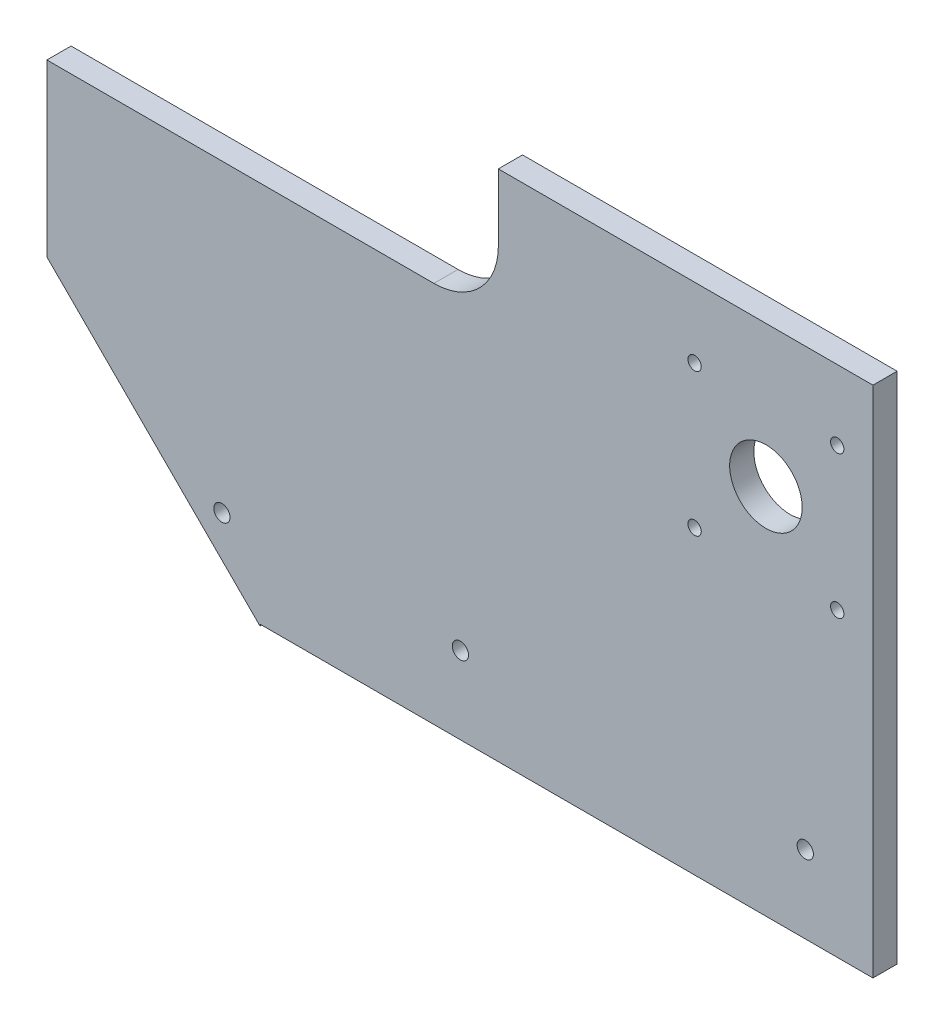
SolidWorks part; units mm, degrees
ref_plane "Front Plane" through (0, 0, 0) normal (0, 0, 1) x (1, 0, 0)
ref_plane "Top Plane" through (0, 0, 0) normal (0, 1, 0) x (1, 0, 0)
ref_plane "Right Plane" through (0, 0, 0) normal (1, 0, 0) x (0, 0, -1)
sketch "Sketch1" plane through (0, 0, 0) normal (0, 0, 1) x (1, 0, 0)
  line L0 (-138.2594, 48.9915) -> (32.2106, -121.4785)
  line L1 (32.2106, -121.4785) -> (222.7106, -121.4785)
  line L2 (-138.2594, 149.5088) -> (-138.2594, 48.9915)
  line L3 (-138.2594, 149.5088) -> (222.7106, 149.5088)
  line L4 (222.7106, -121.4785) -> (222.7106, 149.5088)
  circle A0 centre (180.538, 76.832) radius 14.2875
  circle A2 centre (180.538, 76.832) radius 69.85 construction
  circle A3 centre (180.538, 76.832) radius 318.7974 construction
  point P0 (0, 0)
  point P2 (180.538, 76.832)
  dimension "D4" = 198.3105
  dimension "D1" = 45
  dimension "D2" = 270.9874
  dimension "D5" = 245.11
extrude "Boss-Extrude1" add sketch "Sketch1" along normal blind 9.525
sketch "Sketch2" plane through (0, 0, 9.525) normal (0, 0, 1) x (1, 0, 0)
  line L0 (32.2106, -121.4785) -> (222.7106, -121.4785) construction
  line L1 (241.7606, -121.4785) -> (-18.8123, -121.4785)
  line L2 (241.7606, -121.4785) -> (241.7606, -69.7895)
  line L3 (241.7606, -69.7895) -> (-18.8123, -69.7895)
  line L4 (-18.8123, -121.4785) -> (-18.8123, -69.7895)
extrude "Cut-Extrude1" cut sketch "Sketch2" against normal through all contours L3 L4 L1 L2
sketch "Sketch4" plane through (0, 0, 9.525) normal (0, 0, 1) x (1, 0, 0)
  line L1 (-138.2594, 149.5088) -> (-138.2594, 48.9915) construction
  line L3 (-138.2594, 149.5088) -> (75.1006, 149.5088)
  line L4 (-138.2594, 149.5088) -> (-138.2594, 80.7415)
  line L5 (-138.2594, 80.7415) -> (75.1006, 80.7415)
  line L6 (75.1006, 149.5088) -> (75.1006, 80.7415)
extrude "Cut-Extrude2" cut sketch "Sketch4" against normal through all contours L5 L6 L3 L4
fillet "Fillet2" radius 25.4 2 edges at (-138.2594, 80.7415, 4.7625) (75.1006, 80.7415, 4.7625)
sketch "Sketch16" plane through (222.7106, 0, 0) normal (1, 0, 0) x (0, 0, -1)
  line L0 (0, -69.7895) -> (0, 149.5088) construction
  line L1 (-9.525, 149.5088) -> (0, 149.5088)
  line L2 (-9.525, 149.5088) -> (-9.525, 145.2215)
  line L3 (-9.525, 145.2215) -> (0, 145.2215)
  line L4 (0, 149.5088) -> (0, 145.2215)
extrude "Cut-Extrude3" cut sketch "Sketch16" against normal through all
sketch "Sketch17" plane through (0, 0, 0) normal (0, 0, -1) x (-1, 0, 0)
  line L0 (-222.7106, -69.7895) -> (-222.7106, 145.2215) construction
  line L1 (-75.1006, 145.2215) -> (-222.7106, 145.2215)
  line L2 (-75.1006, 145.2215) -> (-75.1006, 132.5215)
  line L3 (-75.1006, 132.5215) -> (-222.7106, 132.5215)
  line L4 (-222.7106, 145.2215) -> (-222.7106, 132.5215)
  dimension "D1" = 12.7
extrude "Cut-Extrude4" cut sketch "Sketch17" against normal through all
hole_wizard "Tap Drill for M6x0.75 Tap1" positions "Sketch19" profile "Sketch18" hole size "M6x0.75" standard "Lanco STD" end condition through all
sketch "Sketch19" plane through (0, 0, 9.525) normal (0, 0, 1) x (1, 0, 0)
  point P0 (208.638, 104.932)
  point P3 (152.438, 104.932)
  point P6 (152.438, 48.732)
  point P9 (208.638, 48.732)
sketch "Sketch18" plane through (208.638, 104.932, 9.525) normal (1, 0, 0) x (0, -1, 0)
  line L0 (0, 0) -> (0, 9.525)
  line L1 (0, 9.525) -> (2.625, 9.525)
  line L2 (2.625, 9.525) -> (2.625, 0)
  line L5 (2.625, 0) -> (0, 0)
  line L11 (0, -6.35) -> (0, 107.95) construction
  dimension "Thru Hole Dia." = 5.25
  dimension "Thru Hole Depth" = 9.525
hole_wizard "Ø6.4 (6.4) Diameter Hole1" positions "Sketch21" profile "Sketch20" hole size "Ø6.4" standard "ANSI Metric" end condition through all
sketch "Sketch21" plane through (0, 0, 9.525) normal (0, 0, 1) x (1, 0, 0)
  point P0 (196.0406, -39.3145)
  point P2 (60.1506, -39.3145)
  point P4 (-33.8294, -39.3145)
sketch "Sketch20" plane through (196.0406, -39.3145, 9.525) normal (1, 0, 0) x (0, -1, 0)
  line L0 (0, 0) -> (0, 9.525)
  line L1 (0, 9.525) -> (3.2, 9.525)
  line L2 (3.2, 9.525) -> (3.2, 0)
  line L5 (3.2, 0) -> (0, 0)
  line L11 (0, -6.35) -> (0, 107.95) construction
  dimension "Thru Hole Dia." = 6.4
  dimension "Thru Hole Depth" = 9.525
sketch "Sketch22" plane through (0, 0, 9.525) normal (0, 0, 1) x (1, 0, 0)
  line L0 (-102.7904, 145.0855) -> (-102.7904, -100.3395)
  line L1 (222.7106, -69.7895) -> (222.7106, 132.5215) construction
  line L2 (-102.7904, 145.0855) -> (-209.6758, 145.0855)
  line L3 (-209.6758, 145.0855) -> (-209.6758, -95.574)
  line L4 (-209.6758, -95.574) -> (-102.7904, -100.3395)
  dimension "D1" = 325.501
extrude "Cut-Extrude5" cut sketch "Sketch22" against normal through all
